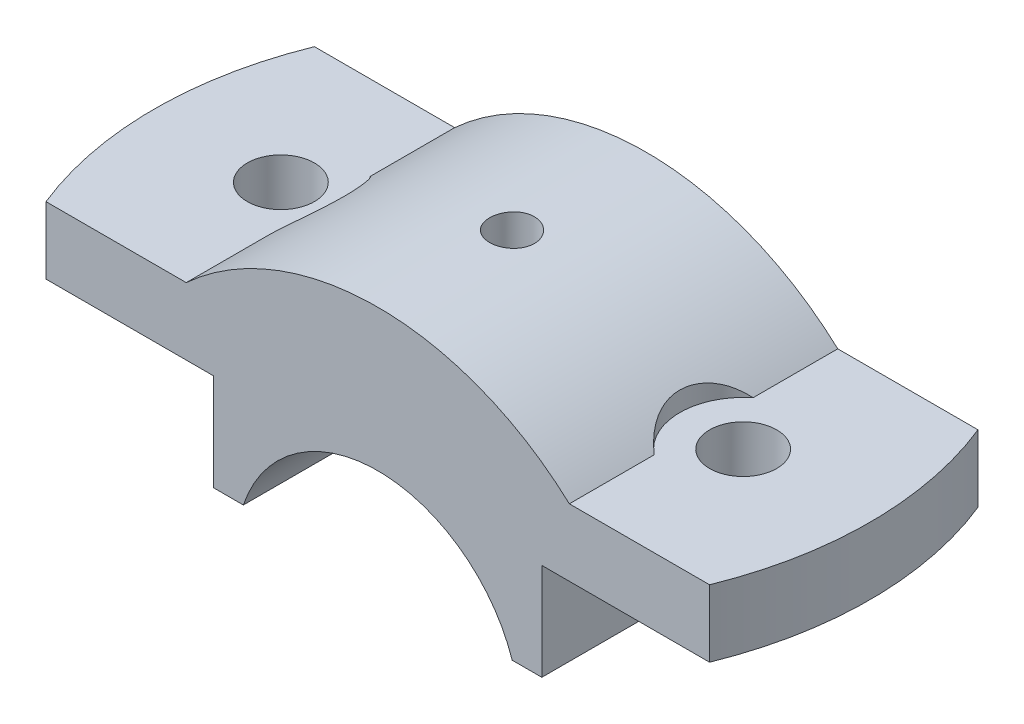
SolidWorks part; units mm, degrees
ref_plane "Front Plane" through (0, 0, 0) normal (0, 0, 1) x (1, 0, 0)
ref_plane "Top Plane" through (0, 0, 0) normal (0, 1, 0) x (1, 0, 0)
ref_plane "Right Plane" through (0, 0, 0) normal (1, 0, 0) x (0, 0, -1)
sketch "Sketch1" plane through (0, 0, 0) normal (0, 0, 1) x (1, 0, 0)
  line L0 (0, 0) -> (0, 86.9938) construction
  line L1 (18.0278, 6) -> (22, 6)
  line L2 (22, 6) -> (22, 19)
  line L3 (22, 19) -> (50, 19)
  line L4 (25.6905, 28) -> (50, 28)
  line L5 (50, 28) -> (50, 19)
  line L6 (-18.0278, 6) -> (-22, 6)
  line L7 (-22, 6) -> (-22, 19)
  line L8 (-22, 19) -> (-50, 19)
  line L9 (-50, 28) -> (-50, 19)
  line L10 (-50, 28) -> (-25.6905, 28)
  arc A0 (18.0278, 6) -> (-18.0278, 6) centre (0, 0) ccw
  arc A1 (25.6905, 28) -> (-25.6905, 28) centre (0, 0) ccw
  point P16 (0, 38)
  dimension "D1" = 19
  dimension "D2" = 38
  dimension "D3" = 44
  dimension "D4" = 13
  dimension "D5" = 9
  dimension "D6" = 19
  dimension "D7" = 50
extrude "Boss-Extrude1" add sketch "Sketch1" along normal mid plane 36
sketch "Sketch2" plane through (0, 28, 0) normal (0, 1, 0) x (1, 0, 0)
  line L1 (-25.6905, -18) -> (-50, -18) construction
  line L2 (-50, -18) -> (-50, 18) construction
  line L3 (-25.6905, 18) -> (-50, 18) construction
  line L4 (-25.6905, -18) -> (-50, -18)
  line L5 (-50, -18) -> (-50, 18)
  line L6 (-25.6905, 18) -> (-50, 18)
  arc A1 (-44.4972, 18) -> (-44.4972, -18) centre (0, 0) ccw
  line M6 (-50, 18) -> (-50, -18)
  line M7 (-50, -18) -> (-25.6905, -18)
  dimension "D2" = 48
extrude "Cut-Extrude3" cut sketch "Sketch2" against normal blind 36 contours A1 L6 M6 M7
sketch "Sketch3" plane through (0, 28, 0) normal (0, 1, 0) x (1, 0, 0)
  circle A0 centre (-31, 0) radius 4.5
  dimension "D1" = 9
  dimension "D2" = 31
extrude "Cut-Extrude4" cut sketch "Sketch3" against normal through all
mirror "Mirror2" about plane through (0, 0, 0) normal (1, 0, 0) of "Cut-Extrude4", "Cut-Extrude3"
sketch "Sketch4" plane through (0, 28, 0) normal (0, 1, 0) x (1, 0, 0)
  line L1 (-25.6905, -18) -> (-25.6905, 18) construction
  line L2 (-25.6905, -6.6377) -> (-25.6905, 6.6377)
  arc A0 (-25.6905, -6.6377) -> (-25.6905, 6.6377) centre (-31, 0) ccw
  circle A1 centre (-31, 0) radius 4.5 construction
  dimension "D2" = 17
extrude "Cut-Extrude5" cut sketch "Sketch4" along normal through all
mirror "Mirror15" about plane through (0, 0, 0) normal (1, 0, 0) of "Cut-Extrude5"
hole_wizard "CBORE for M5 Hex Head Bolt1" positions "3DSketch1" profile "Sketch13" counterbore size "M5" standard "ANSI Metric" end condition through all
sketch3d "3DSketch1"
  point P0 (0, 38, 0)
  dimension "D1" = 0
  dimension "D2" = 0
sketch "Sketch13" plane through (0, 38, 0) normal (1, 0, 0) x (0, 0, 1)
  line L0 (0, 0) -> (0, 32)
  line L1 (0, 32) -> (2.5, 32)
  line L3 (2.5, 32) -> (2.5, 13)
  line L4 (2.5, 13) -> (3, 13)
  line L5 (3, 13) -> (3, 0)
  line L7 (3, 0) -> (0, 0)
  line L11 (0, -6.35) -> (0, 107.95) construction
  dimension "Thru Hole Dia." = 5
  dimension "Thru Hole Depth" = 32
  dimension "C'Bore Dia." = 6
  dimension "C'Bore Depth" = 13
